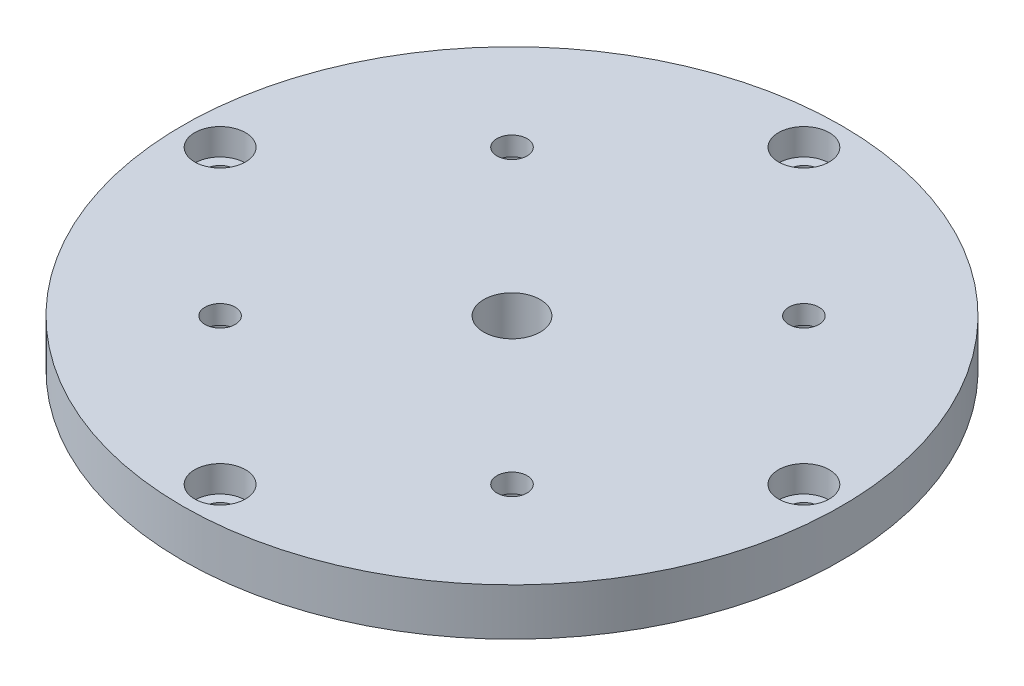
SolidWorks part; units mm, degrees
ref_plane "Front Plane" through (0, 0, 0) normal (0, 0, 1) x (1, 0, 0)
ref_plane "Top Plane" through (0, 0, 0) normal (0, 1, 0) x (1, 0, 0)
ref_plane "Right Plane" through (0, 0, 0) normal (1, 0, 0) x (0, 0, -1)
sketch "Sketch1" plane through (0, 0, 0) normal (0, 1, 0) x (1, 0, 0)
  circle A0 centre (0, 0) radius 35
  circle A1 centre (0, 0) radius 3
extrude "Boss-Extrude1" add sketch "Sketch1" along normal blind 5 contours A1 | A0
sketch "Sketch2" plane through (0, 0, 0) normal (0, -1, 0) x (1, 0, 0)
  line L1 (-15.5, -15.5) -> (15.5, -15.5)
  line L2 (-15.5, -15.5) -> (-15.5, 15.5)
  line L3 (-15.5, 15.5) -> (15.5, 15.5)
  line L4 (15.5, -15.5) -> (15.5, 15.5)
  line L5 (-15.5, -15.5) -> (15.5, 15.5) construction
  line L6 (-15.5, 15.5) -> (15.5, -15.5) construction
  circle A0 centre (15.5, 15.5) radius 1.6
  circle A1 centre (15.5, -15.5) radius 1.6
  circle A2 centre (-15.5, -15.5) radius 1.6
  circle A3 centre (-15.5, 15.5) radius 1.6
  point P0 (0, 0)
  point P16 (0, 0)
  dimension "D1" = 4
extrude "Cut-Extrude1" cut sketch "Sketch2" against normal blind 5 contours A3 | A0 | A1 | A2
sketch "Sketch4" plane through (0, 0, 0) normal (0, -1, 0) x (1, 0, 0)
  circle A0 centre (-15.5, -15.5) radius 1.6 construction
  circle A1 centre (15.5, -15.5) radius 1.6 construction
  circle A2 centre (15.5, 15.5) radius 1.6 construction
  circle A3 centre (-15.5, 15.5) radius 1.6 construction
  circle A4 centre (-15.5, -15.5) radius 1.6
  circle A5 centre (15.5, -15.5) radius 1.6
  circle A6 centre (15.5, 15.5) radius 1.6
  circle A7 centre (-15.5, 15.5) radius 1.6
  circle A8 centre (-15.5, 15.5) radius 2.8
  circle A9 centre (15.5, 15.5) radius 2.8
  circle A10 centre (15.5, -15.5) radius 2.8
  circle A11 centre (-15.5, -15.5) radius 2.8
  dimension "D1" = 1.2
extrude "Cut-Extrude2" cut sketch "Sketch4" against normal blind 3
sketch "Sketch5" plane through (0, 5, 0) normal (0, 1, 0) x (1, 0, 0)
  circle A0 centre (0, 0) radius 31
  circle A1 centre (0, 31) radius 1.6
  circle A2 centre (31, 0) radius 1.6
  circle A3 centre (0, -31) radius 1.6
  circle A4 centre (-31, 0) radius 1.6
  point P14 (0, 0)
  dimension "D1" = 4
extrude "Cut-Extrude3" cut sketch "Sketch5" against normal blind 10 contours A0 A1 | A0 A1 | A2 | A4 | A3
sketch "Sketch6" plane through (0, 5, 0) normal (0, 1, 0) x (1, 0, 0)
  circle A0 centre (0, 31) radius 2.7
  circle A1 centre (31, 0) radius 2.7
  circle A2 centre (0, -31) radius 2.7
  circle A3 centre (-31, 0) radius 2.7
  point P12 (0, 0)
  dimension "D1" = 4
extrude "Cut-Extrude4" cut sketch "Sketch6" against normal blind 2.8
